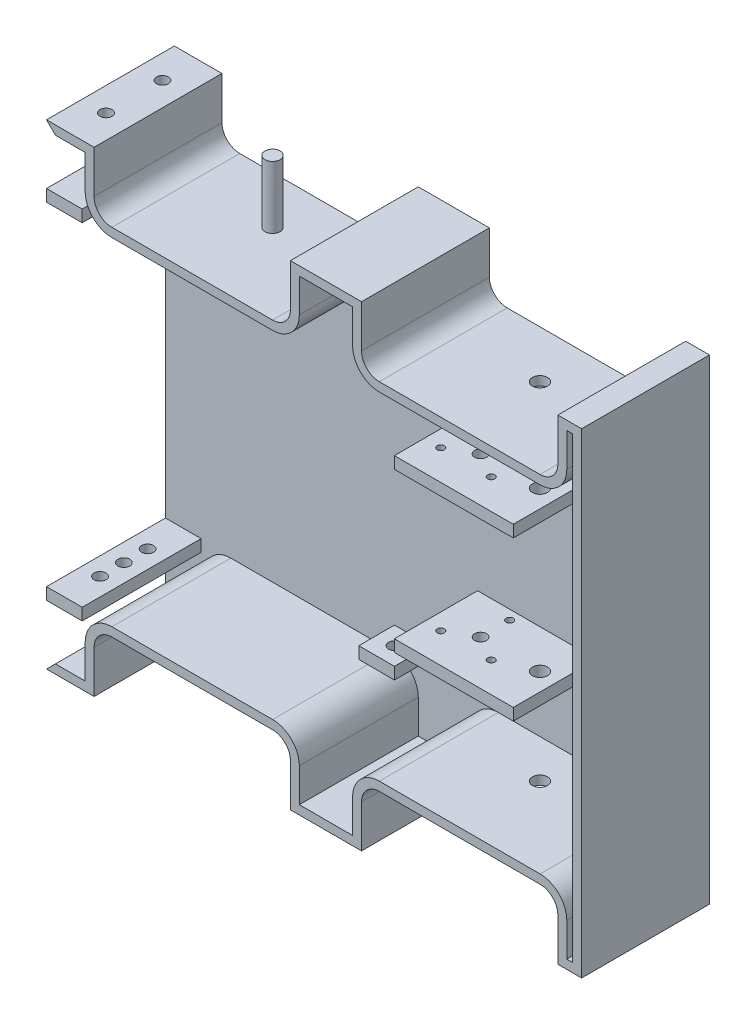
SolidWorks part; units mm, degrees
ref_plane "Front Plane" through (0, 0, 0) normal (0, 0, 1) x (1, 0, 0)
ref_plane "Top Plane" through (0, 0, 0) normal (0, 1, 0) x (1, 0, 0)
ref_plane "Right Plane" through (0, 0, 0) normal (1, 0, 0) x (0, 0, -1)
sketch "Sketch2" plane through (0, 0, 0) normal (0, 0, 1) x (1, 0, 0)
  line L0 (-19.9, 200) -> (39.9, 200)
  line L7 (-225, -200) -> (-185, -200)
  line L8 (-225, -200) -> (-225, 200)
  line L9 (-225, 200) -> (-185, 200)
  line L10 (225, -200) -> (225, 200)
  line L13 (-225, 0) -> (225, 0) construction
  line L14 (39.9, 200) -> (39.9, 164.2)
  line L15 (54.9, 149.2) -> (190, 149.2)
  line L16 (205, 200) -> (205, 164.2)
  line L17 (205, 200) -> (225, 200)
  line L18 (-185, 200) -> (-185, 164.2)
  line L19 (-170, 149.2) -> (-34.9, 149.2)
  line L20 (-19.9, 200) -> (-19.9, 164.2)
  line L21 (205, -200) -> (205, -164.2)
  line L22 (54.9, -149.2) -> (190, -149.2)
  line L23 (39.9, -200) -> (39.9, -164.2)
  line L24 (-19.9, -200) -> (-19.9, -164.2)
  line L25 (-170, -149.2) -> (-34.9, -149.2)
  line L26 (-185, -200) -> (-185, -164.2)
  line L27 (-19.9, -200) -> (39.9, -200)
  line L28 (205, -200) -> (225, -200)
  arc A0 (190, 149.2) -> (205, 164.2) centre (190, 164.2) ccw
  arc A1 (39.9, 164.2) -> (54.9, 149.2) centre (54.9, 164.2) ccw
  arc A2 (-34.9, 149.2) -> (-19.9, 164.2) centre (-34.9, 164.2) ccw
  arc A3 (-170, 149.2) -> (-185, 164.2) centre (-170, 164.2) cw
  arc A4 (190, -149.2) -> (205, -164.2) centre (190, -164.2) cw
  arc A5 (39.9, -164.2) -> (54.9, -149.2) centre (54.9, -164.2) cw
  arc A6 (-34.9, -149.2) -> (-19.9, -164.2) centre (-34.9, -164.2) cw
  arc A7 (-185, -164.2) -> (-170, -149.2) centre (-170, -164.2) cw
  point P0 (0, 0)
  point P6 (0, 0)
  dimension "D11" = 15
  dimension "D7" = 50.8
  dimension "D9" = 15
  dimension "D2" = 165.1
  dimension "D3" = 450
  dimension "D4" = 400
  dimension "D5" = 165.1
  dimension "D6" = 20
  dimension "D8" = 50.8
  dimension "D10" = 40
extrude "Boss-Extrude1" add sketch "Sketch2" along normal blind 7.5
sketch "Sketch4" plane through (0, 0, 7.5) normal (0, 0, 1) x (1, 0, 0)
  line L20 (-217.5, 192.5) -> (-225, 200)
  line L21 (-217.5, -192.5) -> (-225, -200)
  line L40 (217.5, 192.5) -> (212.5, 192.5)
  line L41 (212.5, 192.5) -> (212.5, 164.2)
  line L42 (190, 141.7) -> (54.9, 141.7)
  line L43 (32.4, 164.2) -> (32.4, 192.5)
  line L44 (32.4, 192.5) -> (-12.4, 192.5)
  line L45 (-12.4, 192.5) -> (-12.4, 164.2)
  line L46 (-34.9, 141.7) -> (-170, 141.7)
  line L47 (-192.5, 164.2) -> (-192.5, 192.5)
  line L48 (-192.5, 192.5) -> (-217.5, 192.5)
  line L49 (-217.5, 192.5) -> (-217.5, -192.5)
  line L50 (-217.5, -192.5) -> (-192.5, -192.5)
  line L51 (-192.5, -192.5) -> (-192.5, -164.2)
  line L52 (-170, -141.7) -> (-34.9, -141.7)
  line L53 (-12.4, -164.2) -> (-12.4, -192.5)
  line L54 (-12.4, -192.5) -> (32.4, -192.5)
  line L55 (32.4, -192.5) -> (32.4, -164.2)
  line L56 (54.9, -141.7) -> (190, -141.7)
  line L57 (212.5, -164.2) -> (212.5, -192.5)
  line L58 (212.5, -192.5) -> (217.5, -192.5)
  line L59 (217.5, -192.5) -> (217.5, 192.5)
  line L60 (217.5, 192.5) -> (212.5, 192.5)
  line L61 (212.5, 192.5) -> (212.5, 164.2)
  line L62 (190, 141.7) -> (54.9, 141.7)
  line L63 (32.4, 164.2) -> (32.4, 192.5)
  line L64 (32.4, 192.5) -> (-12.4, 192.5)
  line L65 (-12.4, 192.5) -> (-12.4, 164.2)
  line L66 (-34.9, 141.7) -> (-170, 141.7)
  line L67 (-192.5, 164.2) -> (-192.5, 192.5)
  line L68 (-192.5, 192.5) -> (-217.5, 192.5)
  line L70 (-217.5, -192.5) -> (-192.5, -192.5)
  line L71 (-192.5, -192.5) -> (-192.5, -164.2)
  line L72 (-170, -141.7) -> (-34.9, -141.7)
  line L73 (-12.4, -164.2) -> (-12.4, -192.5)
  line L74 (-12.4, -192.5) -> (32.4, -192.5)
  line L75 (32.4, -192.5) -> (32.4, -164.2)
  line L76 (54.9, -141.7) -> (190, -141.7)
  line L77 (212.5, -164.2) -> (212.5, -192.5)
  line L78 (212.5, -192.5) -> (217.5, -192.5)
  line L79 (217.5, -192.5) -> (217.5, 192.5)
  line L80 (225, 200) -> (205, 200)
  line L81 (205, 200) -> (205, 164.2)
  line L82 (190, 149.2) -> (54.9, 149.2)
  line L83 (39.9, 164.2) -> (39.9, 200)
  line L84 (39.9, 200) -> (-19.9, 200)
  line L85 (-19.9, 200) -> (-19.9, 164.2)
  line L86 (-34.9, 149.2) -> (-170, 149.2)
  line L87 (-185, 164.2) -> (-185, 200)
  line L88 (-185, 200) -> (-225, 200)
  line L89 (-225, 200) -> (-225, -200)
  line L90 (-225, -200) -> (-185, -200)
  line L91 (-185, -200) -> (-185, -164.2)
  line L92 (-170, -149.2) -> (-34.9, -149.2)
  line L93 (-19.9, -164.2) -> (-19.9, -200)
  line L94 (-19.9, -200) -> (39.9, -200)
  line L95 (39.9, -200) -> (39.9, -164.2)
  line L96 (54.9, -149.2) -> (190, -149.2)
  line L97 (205, -164.2) -> (205, -200)
  line L98 (205, -200) -> (225, -200)
  line L99 (225, -200) -> (225, 200)
  line L100 (225, 200) -> (205, 200)
  line L101 (205, 200) -> (205, 164.2)
  line L102 (190, 149.2) -> (54.9, 149.2)
  line L103 (39.9, 164.2) -> (39.9, 200)
  line L104 (39.9, 200) -> (-19.9, 200)
  line L105 (-19.9, 200) -> (-19.9, 164.2)
  line L106 (-34.9, 149.2) -> (-170, 149.2)
  line L107 (-185, 164.2) -> (-185, 200)
  line L108 (-185, 200) -> (-225, 200)
  line L110 (-225, -200) -> (-185, -200)
  line L111 (-185, -200) -> (-185, -164.2)
  line L112 (-170, -149.2) -> (-34.9, -149.2)
  line L113 (-19.9, -164.2) -> (-19.9, -200)
  line L114 (-19.9, -200) -> (39.9, -200)
  line L115 (39.9, -200) -> (39.9, -164.2)
  line L116 (54.9, -149.2) -> (190, -149.2)
  line L117 (205, -164.2) -> (205, -200)
  line L118 (205, -200) -> (225, -200)
  line L119 (225, -200) -> (225, 200)
  arc A16 (190, 141.7) -> (212.5, 164.2) centre (190, 164.2) ccw
  arc A17 (32.4, 164.2) -> (54.9, 141.7) centre (54.9, 164.2) ccw
  arc A18 (-34.9, 141.7) -> (-12.4, 164.2) centre (-34.9, 164.2) ccw
  arc A19 (-192.5, 164.2) -> (-170, 141.7) centre (-170, 164.2) ccw
  arc A20 (-170, -141.7) -> (-192.5, -164.2) centre (-170, -164.2) ccw
  arc A21 (-12.4, -164.2) -> (-34.9, -141.7) centre (-34.9, -164.2) ccw
  arc A22 (54.9, -141.7) -> (32.4, -164.2) centre (54.9, -164.2) ccw
  arc A23 (212.5, -164.2) -> (190, -141.7) centre (190, -164.2) ccw
  arc A24 (190, 141.7) -> (212.5, 164.2) centre (190, 164.2) ccw
  arc A25 (32.4, 164.2) -> (54.9, 141.7) centre (54.9, 164.2) ccw
  arc A26 (-34.9, 141.7) -> (-12.4, 164.2) centre (-34.9, 164.2) ccw
  arc A27 (-192.5, 164.2) -> (-170, 141.7) centre (-170, 164.2) ccw
  arc A28 (-170, -141.7) -> (-192.5, -164.2) centre (-170, -164.2) ccw
  arc A29 (-12.4, -164.2) -> (-34.9, -141.7) centre (-34.9, -164.2) ccw
  arc A30 (54.9, -141.7) -> (32.4, -164.2) centre (54.9, -164.2) ccw
  arc A31 (212.5, -164.2) -> (190, -141.7) centre (190, -164.2) ccw
  arc A32 (190, 149.2) -> (205, 164.2) centre (190, 164.2) ccw
  arc A33 (39.9, 164.2) -> (54.9, 149.2) centre (54.9, 164.2) ccw
  arc A34 (-34.9, 149.2) -> (-19.9, 164.2) centre (-34.9, 164.2) ccw
  arc A35 (-185, 164.2) -> (-170, 149.2) centre (-170, 164.2) ccw
  arc A36 (-170, -149.2) -> (-185, -164.2) centre (-170, -164.2) ccw
  arc A37 (-19.9, -164.2) -> (-34.9, -149.2) centre (-34.9, -164.2) ccw
  arc A38 (54.9, -149.2) -> (39.9, -164.2) centre (54.9, -164.2) ccw
  arc A39 (205, -164.2) -> (190, -149.2) centre (190, -164.2) ccw
  arc A40 (190, 149.2) -> (205, 164.2) centre (190, 164.2) ccw
  arc A41 (39.9, 164.2) -> (54.9, 149.2) centre (54.9, 164.2) ccw
  arc A42 (-34.9, 149.2) -> (-19.9, 164.2) centre (-34.9, 164.2) ccw
  arc A43 (-185, 164.2) -> (-170, 149.2) centre (-170, 164.2) ccw
  arc A44 (-170, -149.2) -> (-185, -164.2) centre (-170, -164.2) ccw
  arc A45 (-19.9, -164.2) -> (-34.9, -149.2) centre (-34.9, -164.2) ccw
  arc A46 (54.9, -149.2) -> (39.9, -164.2) centre (54.9, -164.2) ccw
  arc A47 (205, -164.2) -> (190, -149.2) centre (190, -164.2) ccw
  dimension "D1" = 7.5
  dimension "D2" = 0
extrude "Boss-Extrude3" add sketch "Sketch4" along normal blind 100
sketch "Sketch5" plane through (0, -149.2, 0) normal (0, -1, 0) x (1, 0, 0)
  line L0 (-225, 40) -> (225, 40) construction
  line L1 (-225, 107.5) -> (-225, 7.5) construction
  line L2 (225, 107.5) -> (225, 0) construction
  line L3 (54.9, 0) -> (190, 0) construction
  line L4 (54.9, 53.75) -> (190, 53.75) construction
  line L5 (54.9, 107.5) -> (54.9, 0) construction
  line L6 (190, 107.5) -> (190, 0) construction
  line L7 (-170, 53.75) -> (-34.9, 53.75) construction
  line L8 (-170, 107.5) -> (-170, 0) construction
  line L9 (-34.9, 107.5) -> (-34.9, 0) construction
  line L10 (-102.45, 107.5) -> (-102.45, 0) construction
  line L11 (-170, 107.5) -> (-34.9, 107.5) construction
  line L12 (-170, 0) -> (-34.9, 0) construction
  line L13 (122.45, 107.5) -> (122.45, 0) construction
  line L14 (54.9, 107.5) -> (190, 107.5) construction
  circle A0 centre (-102.45, 40) radius 6.35
  circle A1 centre (122.45, 40) radius 6.35
  dimension "D2" = 12.7
  dimension "D1" = 40
extrude "Cut-Extrude1" cut sketch "Sketch5" against normal blind 335
sketch "Sketch6" plane through (0, 0, 7.5) normal (0, 0, 1) x (1, 0, 0)
  line L0 (54.9, 141.7) -> (190, 141.7) construction
  line L1 (37.5, 71.7) -> (137.5, 71.7)
  line L2 (37.5, 71.7) -> (37.5, 61.7)
  line L3 (37.5, 61.7) -> (137.5, 61.7)
  line L4 (137.5, 71.7) -> (137.5, 61.7)
  line L5 (217.5, 192.5) -> (217.5, -192.5) construction
  line L6 (-225, 0) -> (225, 0) construction
  line L7 (-225, 200) -> (-225, -200) construction
  line L8 (225, -200) -> (225, 200) construction
  line L9 (37.5, -61.7) -> (137.5, -61.7)
  line L10 (37.5, -71.7) -> (37.5, -61.7)
  line L11 (137.5, -71.7) -> (137.5, -61.7)
  line L12 (37.5, -71.7) -> (137.5, -71.7)
  point P13 (0, 0)
  dimension "D1" = 70
  dimension "D2" = 10
  dimension "D3" = 100
  dimension "D4" = 80
extrude "Boss-Extrude4" add sketch "Sketch6" along normal blind 70
sketch "Sketch7" plane through (0, -149.2, 0) normal (0, -1, 0) x (1, 0, 0)
  circle A0 centre (122.45, 40) radius 6.35 construction
  circle A1 centre (122.45, 40) radius 6.35
extrude "Cut-Extrude2" cut sketch "Sketch7" against normal blind 322
sketch "Sketch9" plane through (0, 61.7, 0) normal (0, -1, 0) x (1, 0, 0)
  line L0 (122.45, 40) -> (37.5, 40) construction
  line L1 (37.5, 77.5) -> (37.5, 7.5) construction
  circle A0 centre (72.5, 40) radius 24.5 construction
  circle A1 centre (72.5, 15.5) radius 3
  circle A2 centre (51.2824, 52.25) radius 3
  circle A3 centre (93.7176, 52.25) radius 3
  circle A4 centre (72.5, 40) radius 5
  point P15 (72.5, 40)
  dimension "D1" = 49
  dimension "D3" = 6
  dimension "D5" = 10
  dimension "D2" = 35
  dimension "D4" = 3
extrude "Cut-Extrude3" cut sketch "Sketch9" against normal blind 53
mirror "Mirror1" about plane through (0, 0, 0) normal (0, 1, 0) of "Cut-Extrude3"
sketch "Sketch10" plane through (0, -141.7, 0) normal (0, 1, 0) x (1, 0, 0)
  circle A0 centre (-102.45, -40) radius 6.35 construction
  circle A1 centre (-102.45, -40) radius 6.35
extrude "Boss-Extrude5" add sketch "Sketch10" against normal blind 60
mirror "Mirror2" about plane through (0, 0, 0) normal (0, 1, 0) of "Boss-Extrude5"
sketch "Sketch11" plane through (0, -200, 0) normal (0, -1, 0) x (1, 0, 0)
  line L0 (-205, 107.5) -> (-205, 0) construction
  line L1 (-225, 107.5) -> (-185, 107.5) construction
  line L2 (-225, 0) -> (-185, 0) construction
  circle A0 centre (-205, 77.5) radius 5
  circle A1 centre (-205, 30) radius 5
  dimension "D1" = 10
  dimension "D2" = 10
  dimension "D3" = 30
  dimension "D4" = 30
extrude "Cut-Extrude4" cut sketch "Sketch11" against normal blind 490
sketch "Sketch12" plane through (0, 0, 7.5) normal (0, 0, 1) x (1, 0, 0)
  line L0 (-170, 141.7) -> (-34.9, 141.7) construction
  line L1 (-32.4, 121.7) -> (-2.4, 121.7)
  line L2 (-32.4, 121.7) -> (-32.4, 131.7)
  line L3 (-32.4, 131.7) -> (-2.4, 131.7)
  line L4 (-2.4, 121.7) -> (-2.4, 131.7)
  line L5 (-32.4, 121.7) -> (-2.4, 131.7) construction
  line L6 (-32.4, 131.7) -> (-2.4, 121.7) construction
  line L7 (-12.4, 164.2) -> (-12.4, 192.5) construction
  point P0 (-17.4, 126.7)
  dimension "D1" = 10
  dimension "D2" = 30
  dimension "D3" = 10
  dimension "D4" = 10
extrude "Boss-Extrude6" add sketch "Sketch12" along normal blind 30
sketch "Sketch13" plane through (0, 121.7, 0) normal (0, -1, 0) x (1, 0, 0)
  line L0 (-17.4, 37.5) -> (-17.4, 7.5) construction
  line L1 (-32.4, 37.5) -> (-2.4, 37.5) construction
  line L2 (-32.4, 7.5) -> (-2.4, 7.5) construction
  circle A0 centre (-17.4, 22.5) radius 5
  dimension "D1" = 10
extrude "Cut-Extrude5" cut sketch "Sketch13" against normal blind 10
mirror "Mirror3" about plane through (0, 0, 0) normal (0, 1, 0) of "Cut-Extrude5", "Boss-Extrude6"
sketch "Sketch14" plane through (0, 0, 7.5) normal (0, 0, 1) x (1, 0, 0)
  line L1 (-225, 140) -> (-195, 140)
  line L2 (-225, 140) -> (-225, 150)
  line L3 (-225, 150) -> (-195, 150)
  line L4 (-195, 140) -> (-195, 150)
  line L5 (-225, 140) -> (-195, 150) construction
  line L6 (-225, 150) -> (-195, 140) construction
  line L7 (-185, 200) -> (-225, 200) construction
  line L8 (-225, 200) -> (-225, -200) construction
  point P0 (-210, 145)
  point P9 (-205, 200)
  dimension "D1" = 50
  dimension "D2" = 10
  dimension "D3" = 30
  dimension "D4" = 15
extrude "Boss-Extrude7" add sketch "Sketch14" along normal blind 100
sketch "Sketch15" plane through (0, 140, 0) normal (0, -1, 0) x (1, 0, 0)
  line L0 (-210, 107.5) -> (-210, 7.5) construction
  line L1 (-225, 107.5) -> (-195, 107.5) construction
  line L2 (-225, 7.5) -> (-195, 7.5) construction
  circle A0 centre (-210, 77.5) radius 5
  circle A1 centre (-210, 57.5) radius 5
  circle A2 centre (-210, 37.5) radius 5
  dimension "D1" = 10
  dimension "D2" = 30
  dimension "D3" = 20
  dimension "D4" = 20
extrude "Cut-Extrude6" cut sketch "Sketch15" against normal blind 35
mirror "Mirror4" about plane through (0, 0, 0) normal (0, 1, 0) of "Boss-Extrude7", "Cut-Extrude6"
